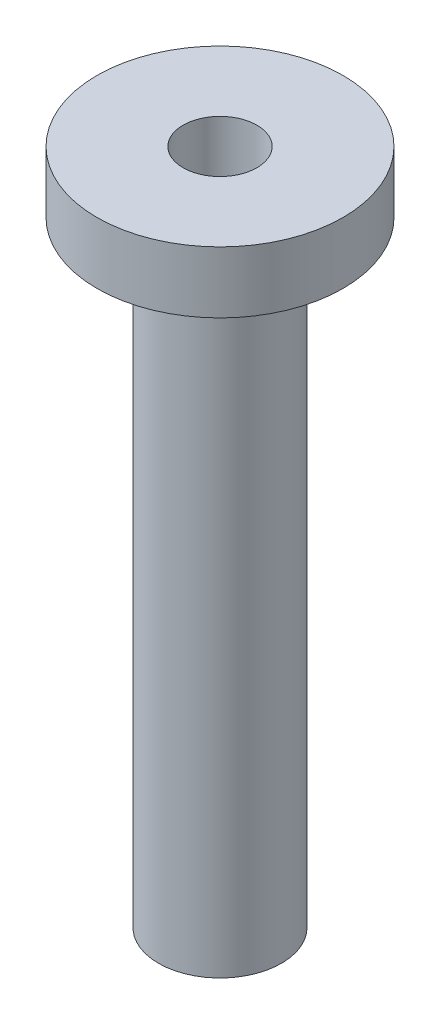
SolidWorks part; units mm, degrees
ref_plane "Front Plane" through (0, 0, 0) normal (0, 0, 1) x (1, 0, 0)
ref_plane "Top Plane" through (0, 0, 0) normal (0, 1, 0) x (1, 0, 0)
ref_plane "Right Plane" through (0, 0, 0) normal (1, 0, 0) x (0, 0, -1)
sketch "Sketch1" plane through (0, 0, 0) normal (0, 0, 1) x (1, 0, 0)
  line L0 (-3.81, 0) -> (-12.7, 0)
  line L1 (-12.7, 0) -> (-12.7, -6.35)
  line L2 (-12.7, -6.35) -> (-11.1125, -6.35)
  line L3 (-11.1125, -6.35) -> (-11.1125, -4.318)
  line L4 (-11.1125, -4.318) -> (-8.0645, -4.318)
  line L5 (-8.0645, -4.318) -> (-8.0645, -6.35)
  line L6 (-8.0645, -6.35) -> (-6.35, -6.35)
  line L7 (-6.35, -6.35) -> (-6.35, -69.85)
  line L8 (-6.35, -69.85) -> (-3.81, -67.31)
  line L9 (-3.81, -67.31) -> (-3.81, 0)
  line L10 (0, 0) -> (0, -4.7723) construction
  dimension "D1" = 1.5875
  dimension "D2" = 2.032
  dimension "D3" = 3.048
  dimension "D4" = 12.7
  dimension "D5" = 3.81
  dimension "D6" = 6.35
  dimension "D7" = 45
  dimension "D8" = 63.5
  dimension "D9" = 6.35
revolve "Revolve1" add sketch "Sketch1" angle 360 about L10
